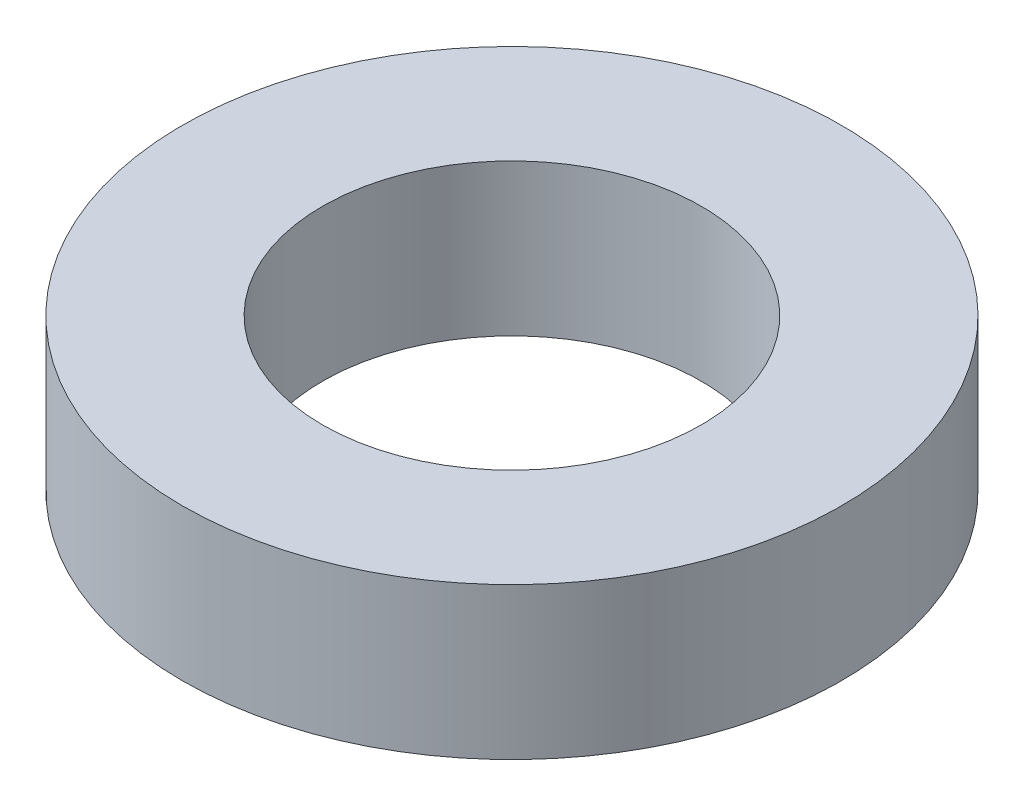
SolidWorks part; units mm, degrees
material "6061 Alloy"
ref_plane "Front Plane" through (0, 0, 0) normal (0, 0, 1) x (1, 0, 0)
ref_plane "Top Plane" through (0, 0, 0) normal (0, 1, 0) x (1, 0, 0)
ref_plane "Right Plane" through (0, 0, 0) normal (1, 0, 0) x (0, 0, -1)
sketch "Sketch1" plane through (0, 0, 0) normal (0, 1, 0) x (1, 0, 0)
  circle A0 centre (0, 0) radius 11.049
  circle A1 centre (0, 0) radius 6.35
  dimension "D1" = 22.098
  dimension "D2" = 12.7
extrude "Boss-Extrude1" add sketch "Sketch1" along normal blind 5.08
